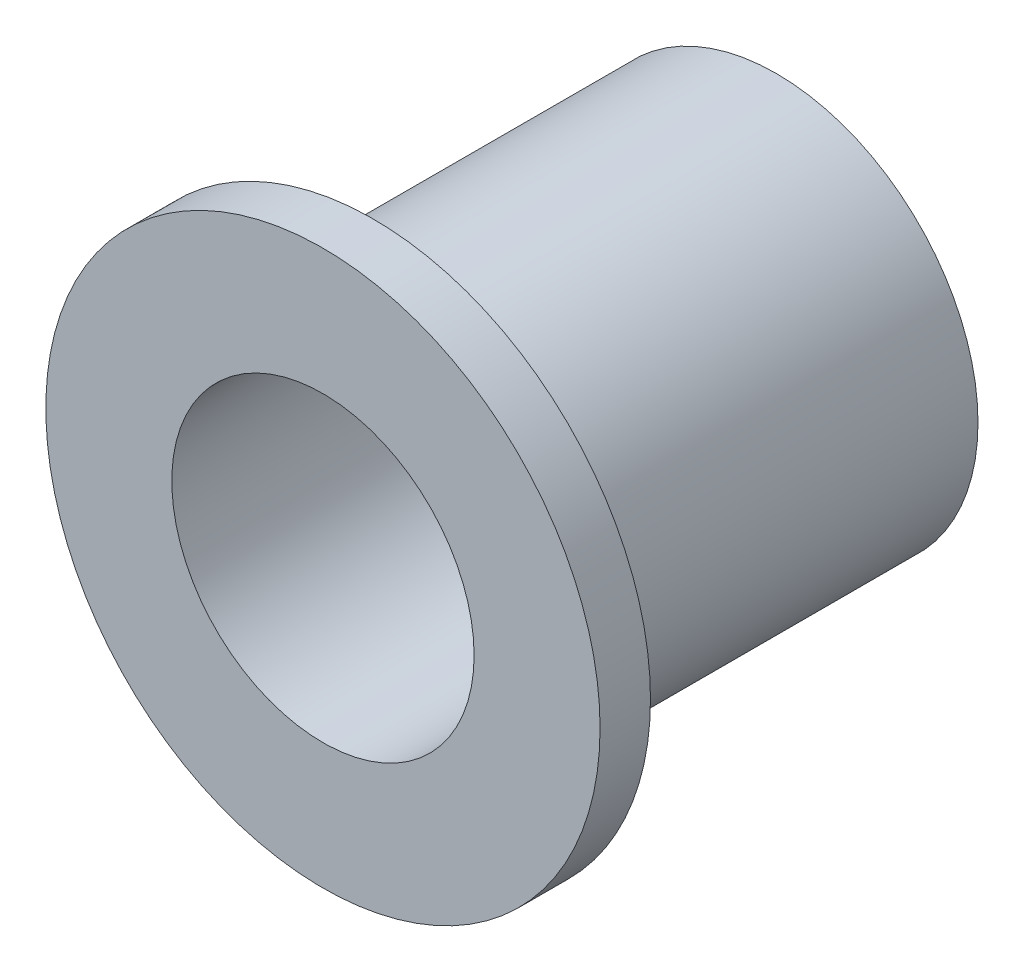
SolidWorks part; units mm, degrees
ref_plane "Front Plane" through (0, 0, 0) normal (0, 0, 1) x (1, 0, 0)
ref_plane "Top Plane" through (0, 0, 0) normal (0, 1, 0) x (1, 0, 0)
ref_plane "Right Plane" through (0, 0, 0) normal (1, 0, 0) x (0, 0, -1)
sketch "Sketch1" plane through (0, 0, 0) normal (0, 0, 1) x (1, 0, 0)
  circle A0 centre (0, 0) radius 8.7312
  dimension "D1" = 17.4625
extrude "Boss-Extrude1" add sketch "Sketch1" along normal blind 1.5875
sketch "Sketch2" plane through (0, 0, 0) normal (0, 0, -1) x (-1, 0, 0)
  circle A0 centre (0, 0) radius 6.35
  dimension "D1" = 12.7
extrude "Boss-Extrude2" add sketch "Sketch2" along normal blind 12.7
sketch "Sketch3" plane through (0, 0, 1.5875) normal (0, 0, 1) x (1, 0, 0)
  circle A0 centre (0, 0) radius 4.7625
  dimension "D1" = 9.525
extrude "Cut-Extrude1" cut sketch "Sketch3" against normal through all
